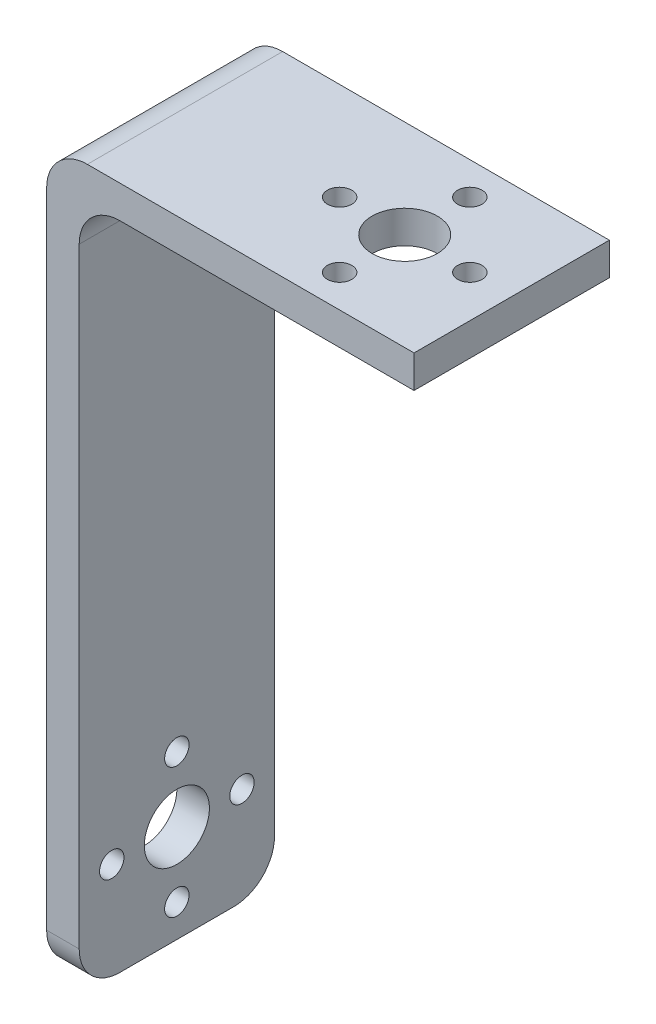
SolidWorks part; units mm, degrees
material "Acrylic (Medium-high impact)"
ref_plane "Front Plane" through (0, 0, 0) normal (0, 0, 1) x (1, 0, 0)
ref_plane "Top Plane" through (0, 0, 0) normal (0, 1, 0) x (1, 0, 0)
ref_plane "Right Plane" through (0, 0, 0) normal (1, 0, 0) x (0, 0, -1)
sketch "Sketch1" plane through (0, 0, 0) normal (0, 0, 1) x (1, 0, 0)
  line L0 (-35.9477, -38.738) -> (-35.9477, 46.262)
  line L1 (-35.9477, 46.262) -> (5.1971, 46.262)
  line L3 (-39.9477, -38.738) -> (-39.9477, 50.262)
  line L4 (-39.9477, 50.262) -> (5.1971, 50.262)
  line L5 (-35.9477, 46.262) -> (20.0523, 46.262) construction
  line L6 (-39.9477, -38.738) -> (-35.9477, -38.738)
  line L7 (-39.9477, 50.262) -> (24.0523, 50.262) construction
  line L9 (5.1971, 46.262) -> (5.1971, 50.262)
  line L11 (20.0523, 46.262) -> (20.0523, -38.738) construction
  line L12 (24.0523, 50.262) -> (24.0523, -38.738) construction
  dimension "D1" = 4
extrude "Boss-Extrude1" add sketch "Sketch1" along normal blind 24
sketch "Sketch3" plane through (-39.9477, 0, 0) normal (-1, 0, 0) x (0, 0, 1)
  line L0 (0, -38.738) -> (0, 50.262) construction
  line L1 (24, -38.738) -> (0, -38.738) construction
  line L2 (12, -26.738) -> (20, -26.738)
  circle A0 centre (12, -26.738) radius 4
  circle A1 centre (20, -26.738) radius 1.5
  circle A2 centre (12, -34.738) radius 1.5
  circle A3 centre (4, -26.738) radius 1.5
  circle A4 centre (12, -18.738) radius 1.5
  point P17 (12, -26.738)
  dimension "D1" = 12
  dimension "D3" = 4
  dimension "D2" = 12
extrude "Cut-Extrude2" cut sketch "Sketch3" against normal blind 4 contours A4 | A1 | A0 | A2 | A3
sketch "Sketch6" plane through (0, 50.262, 0) normal (0, 1, 0) x (1, 0, 0)
  line L3 (-39.9477, -24) -> (5.1971, -24) construction
  line L4 (-39.9477, -24) -> (-39.9477, 0) construction
  circle A0 centre (-7.9477, -12) radius 4
  circle A1 centre (0.0523, -12) radius 1.5
  circle A2 centre (-7.9477, -20) radius 1.5
  circle A3 centre (-7.9477, -12) radius 4
  circle A4 centre (-15.9477, -12) radius 1.5
  circle A5 centre (-7.9477, -12) radius 4
  circle A6 centre (-7.9477, -4) radius 1.5
  circle A7 centre (-7.9477, -12) radius 4
  point P6 (-39.9477, -12)
  point P25 (-7.9477, -12)
  dimension "D1" = 12
  dimension "D3" = 4
  dimension "D2" = 32
extrude "Cut-Extrude3" cut sketch "Sketch6" against normal blind 4 contours A6 | A1 | A2 | A4 | A0
fillet "Fillet1" radius 5 4 edges at (-35.9477, 46.262, 12) (-39.9477, 50.262, 12) (-37.9477, -38.738, 0) (-37.9477, -38.738, 24)
